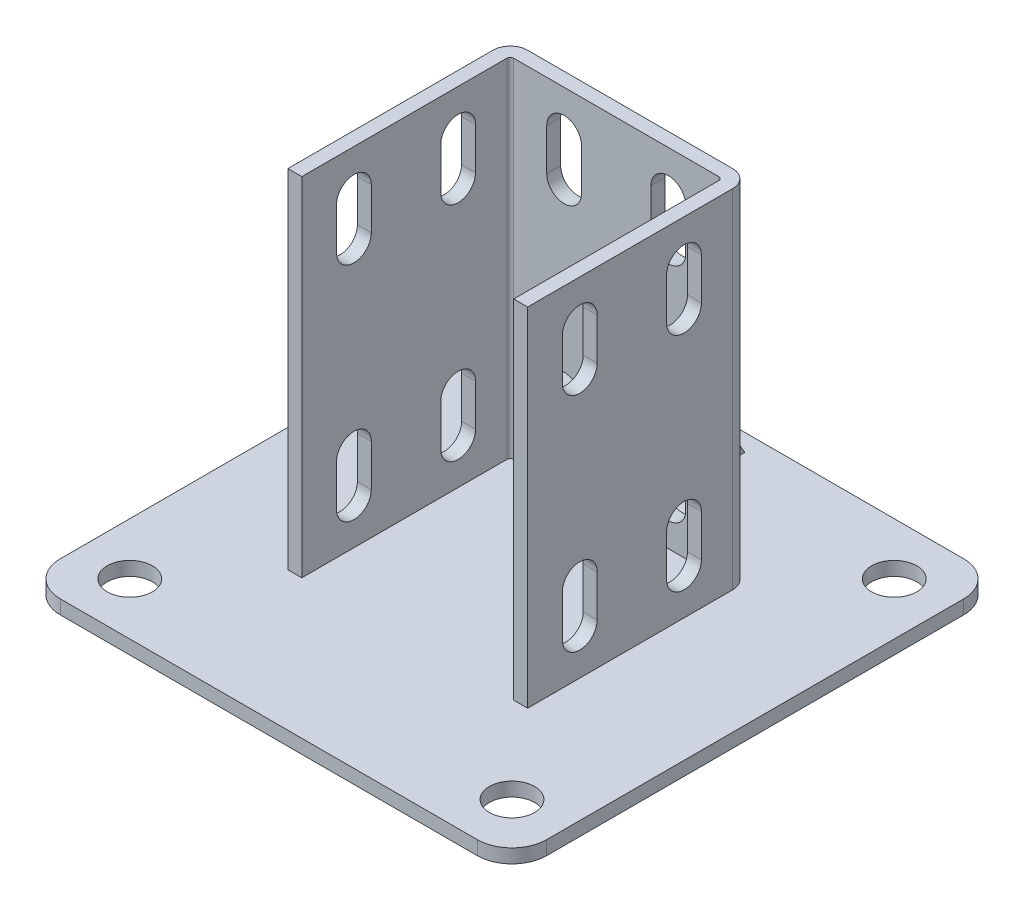
SolidWorks part; units mm, degrees
material "Ст3пс ГОСТ 380-2005"
ref_plane "Спереди" through (0, 0, 0) normal (0, 0, 1) x (1, 0, 0)
ref_plane "Сверху" through (0, 0, 0) normal (0, 1, 0) x (1, 0, 0)
ref_plane "Справа" through (0, 0, 0) normal (1, 0, 0) x (0, 0, -1)
sketch "Эскиз2" plane through (0, 0, 0) normal (0, 1, 0) x (1, 0, 0)
  line L1 (-70, -70) -> (70, -70)
  line L2 (-70, -70) -> (-70, 70)
  line L3 (-70, 70) -> (70, 70)
  line L4 (70, -70) -> (70, 70)
  line L5 (-70, -70) -> (70, 70) construction
  line L6 (-70, 70) -> (70, -70) construction
  point P0 (0, 0)
  dimension "D2" = 140
extrude "Бобышка-Вытянуть1" add sketch "Эскиз2" along normal blind 4
sketch "Эскиз3" plane through (0, 4, 0) normal (0, 1, 0) x (1, 0, 0)
  line L0 (-30.5, -30) -> (-30.5, 30)
  line L1 (-30.5, 30) -> (30.5, 30)
  line L2 (30.5, 30) -> (30.5, -30)
  point P2 (0, 30)
  point P5 (-30.5, 0)
  dimension "D2" = 61
  dimension "D3" = 60
extrude "Вытянуть-Тонкостенный1" add sketch "Эскиз3" along normal offset from surface (100 mm away) 104 thin up to face at (0, 0, 0) thin type one direction reverse wall 4
sketch "Эскиз4" plane through (0, 0, 0) normal (1, 0, 0) x (0, 0, -1)
  line L0 (34, 57.6936) -> (65, 4)
  line L1 (34, 104) -> (34, 4) construction
  line L2 (-70, 4) -> (70, 4) construction
  line L3 (65, 4) -> (34, 4)
  line L4 (34, 4) -> (34, 57.6936)
  line L5 (70, 4) -> (70, 0) construction
  dimension "D1" = 30
  dimension "D2" = 5
extrude "Бобышка-Вытянуть2" add sketch "Эскиз4" along normal mid plane 4
sketch "Эскиз5" plane through (34.5, 0, 0) normal (1, 0, 0) x (0, 0, -1)
  line L0 (-15, 92) -> (-15, 80) construction
  line L1 (-10, 92) -> (-10, 80)
  line L2 (-20, 92) -> (-20, 80)
  line L3 (-15, 28) -> (-15, 16) construction
  line L4 (-10, 28) -> (-10, 16)
  line L5 (-20, 28) -> (-20, 16)
  line L6 (-30, 104) -> (29, 104) construction
  line L7 (-70, 4) -> (70, 4) construction
  line L8 (0, 0) -> (0, 63.8564) construction
  line L11 (15, 92) -> (15, 80) construction
  line L14 (10, 92) -> (10, 80)
  line L15 (20, 92) -> (20, 80)
  line L16 (15, 28) -> (15, 16) construction
  line L17 (10, 28) -> (10, 16)
  line L18 (20, 28) -> (20, 16)
  arc A0 (-10, 92) -> (-20, 92) centre (-15, 92) ccw
  arc A1 (-20, 80) -> (-10, 80) centre (-15, 80) ccw
  arc A2 (-10, 28) -> (-20, 28) centre (-15, 28) ccw
  arc A3 (-20, 16) -> (-10, 16) centre (-15, 16) ccw
  arc A8 (10, 92) -> (20, 92) centre (15, 92) cw
  arc A9 (20, 80) -> (10, 80) centre (15, 80) cw
  arc A10 (10, 28) -> (20, 28) centre (15, 28) cw
  arc A11 (20, 16) -> (10, 16) centre (15, 16) cw
  point P3 (-15, 86)
  point P8 (-15, 22)
  point P22 (15, 86)
  point P29 (15, 22)
extrude "Вырез-Вытянуть1" cut sketch "Эскиз5" against normal through all
sketch "Эскиз6" plane through (0, 4, 0) normal (0, 1, 0) x (1, 0, 0)
  line L0 (-70, 70) -> (-70, -70) construction
  line L1 (55, -55) -> (-55, -55) construction
  line L2 (55, -55) -> (55, 55) construction
  line L3 (55, 55) -> (-55, 55) construction
  line L4 (-55, -55) -> (-55, 55) construction
  line L5 (55, -55) -> (-55, 55) construction
  line L6 (55, 55) -> (-55, -55) construction
  line L7 (70, 70) -> (-70, 70) construction
  circle A0 centre (-55, 55) radius 6.5
  circle A1 centre (-55, -55) radius 6.5
  circle A2 centre (55, 55) radius 6.5
  circle A3 centre (55, -55) radius 6.5
  point P0 (0, 0)
  dimension "D1" = 13
  dimension "D2" = 15
  dimension "D3" = 15
extrude "Вырез-Вытянуть2" cut sketch "Эскиз6" against normal through all
fillet "Скругление1" radius 10 4 edges at (70, 2, 70) (-70, 2, 70) (-70, 2, -70) (70, 2, -70)
sketch "Эскиз8" plane through (0, 0, -34) normal (0, 0, -1) x (-1, 0, 0)
  line L0 (-15, 92) -> (-15, 80) construction
  line L1 (-10, 92) -> (-10, 80)
  line L2 (-20, 92) -> (-20, 80)
  line L3 (-15, 28) -> (-15, 16) construction
  line L4 (-10, 28) -> (-10, 16)
  line L5 (-20, 28) -> (-20, 16)
  line L6 (-29.5, 104) -> (29.5, 104) construction
  line L7 (-60, 4) -> (60, 4) construction
  line L8 (0, 0) -> (0, 80) construction
  line L9 (-60, 0) -> (60, 0) construction
  line L10 (15, 92) -> (15, 80) construction
  line L11 (10, 92) -> (10, 80)
  line L12 (20, 92) -> (20, 80)
  line L13 (15, 28) -> (15, 16) construction
  line L14 (10, 28) -> (10, 16)
  line L15 (20, 28) -> (20, 16)
  arc A0 (-10, 92) -> (-20, 92) centre (-15, 92) ccw
  arc A1 (-20, 80) -> (-10, 80) centre (-15, 80) ccw
  arc A2 (-10, 28) -> (-20, 28) centre (-15, 28) ccw
  arc A3 (-20, 16) -> (-10, 16) centre (-15, 16) ccw
  arc A4 (10, 92) -> (20, 92) centre (15, 92) cw
  arc A5 (20, 80) -> (10, 80) centre (15, 80) cw
  arc A6 (10, 28) -> (20, 28) centre (15, 28) cw
  arc A7 (20, 16) -> (10, 16) centre (15, 16) cw
  point P2 (-15, 86)
  point P7 (-15, 22)
  point P24 (15, 86)
  point P31 (15, 22)
extrude "Вырез-Вытянуть3" cut sketch "Эскиз8" against normal up to next
equation "\"D5@Эскиз5\"=\"D5@Эскиз8\""
